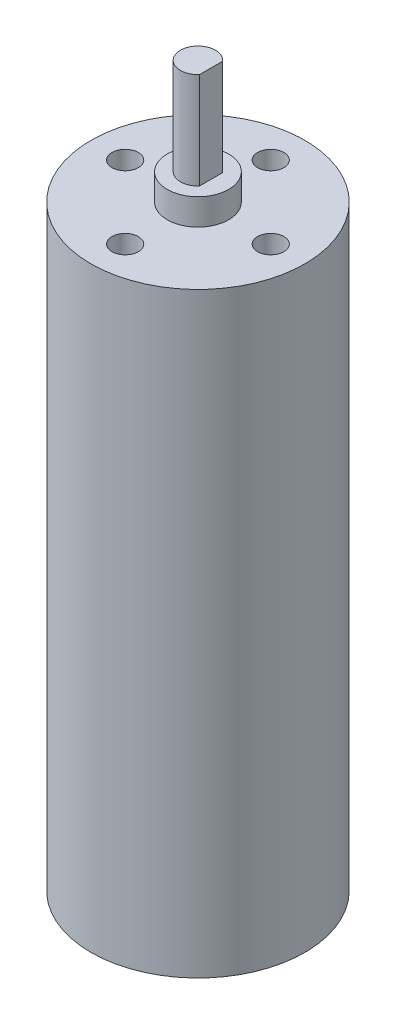
SolidWorks part; units mm, degrees
ref_plane "Front Plane" through (0, 0, 0) normal (0, 0, 1) x (1, 0, 0)
ref_plane "Top Plane" through (0, 0, 0) normal (0, 1, 0) x (1, 0, 0)
ref_plane "Right Plane" through (0, 0, 0) normal (1, 0, 0) x (0, 0, -1)
sketch "Sketch1" plane through (0, 0, 0) normal (0, 1, 0) x (1, 0, 0)
  circle A0 centre (0, 0) radius 12.2
  dimension "D1" = 24.4
extrude "Boss-Extrude1" add sketch "Sketch1" along normal blind 47 contours A0
sketch "Sketch2" plane through (0, 47, 0) normal (0, 1, 0) x (1, 0, 0)
  circle A0 centre (0, 0) radius 12.2
extrude "Boss-Extrude3" add sketch "Sketch2" along normal blind 21
sketch "Sketch3" plane through (0, 68, 0) normal (0, 1, 0) x (1, 0, 0)
  circle A0 centre (0, 0) radius 3.5
  dimension "D1" = 7
extrude "Boss-Extrude4" add sketch "Sketch3" along normal blind 3 contours A0
sketch "Sketch4" plane through (0, 71, 0) normal (0, 1, 0) x (1, 0, 0)
  line L0 (1.5, 1.3229) -> (1.5, -1.3229)
  arc A0 (1.5, 1.3229) -> (1.5, -1.3229) centre (0, 0) ccw
  dimension "D1" = 4
  dimension "D2" = 1.5
extrude "Boss-Extrude5" add sketch "Sketch4" along normal blind 11
sketch "Sketch5" plane through (0, 0, 0) normal (0, -1, 0) x (-1, 0, 0)
  text T0 "TSINY\r\nTS-25GA" font "Century Gothic" height 2
sketch "Sketch6" plane through (0, 0, 0) normal (0, -1, 0) x (1, 0, 0)
  circle A0 centre (8.05, -5.4) radius 1
  circle A1 centre (-8.05, -5.4) radius 1
  circle A2 centre (0, 0) radius 12.2 construction
  dimension "D5" = 2
  dimension "D6" = 2
  dimension "D1" = 8.05
  dimension "D2" = 8.05
  dimension "D3" = 5.4
  dimension "D4" = 5.4
extrude "Cut-Extrude1" cut sketch "Sketch6" against normal blind 10
extrude "Cut-Extrude2" cut sketch "Sketch5" against normal blind 4
sketch "Sketch7" plane through (0, 68, 0) normal (0, 1, 0) x (1, 0, 0)
  circle A0 centre (0, 8.3) radius 1.5
  circle A1 centre (0, -8.3) radius 1.5
  circle A3 centre (8.3, 0) radius 1.5
  circle A4 centre (-8.3, 0) radius 1.5
  dimension "D3" = 3
  dimension "D4" = 3
  dimension "D7" = 3
  dimension "D8" = 3
  dimension "D1" = 8.3
  dimension "D2" = 8.3
  dimension "D5" = 8.3
  dimension "D6" = 8.3
extrude "Cut-Extrude3" cut sketch "Sketch7" against normal blind 10
